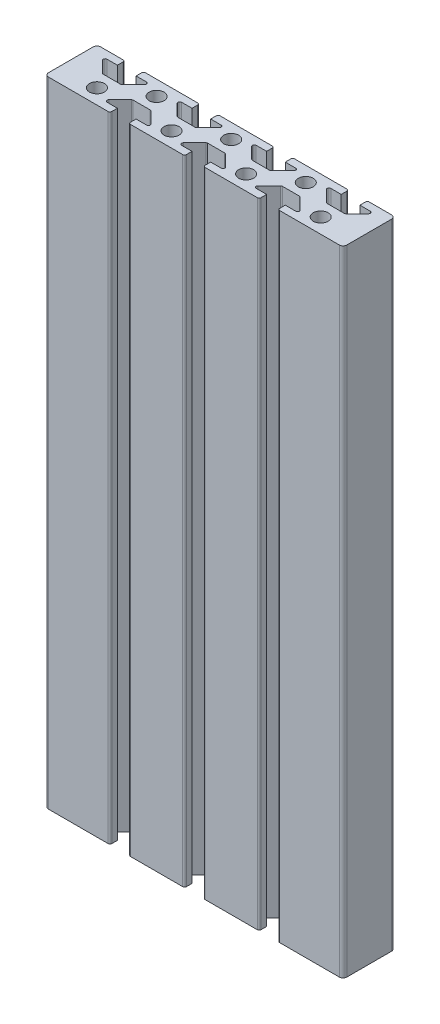
SolidWorks part; units mm, degrees
ref_plane "Front Plane" through (0, 0, 0) normal (0, 0, 1) x (1, 0, 0)
ref_plane "Top Plane" through (0, 0, 0) normal (0, 1, 0) x (1, 0, 0)
ref_plane "Right Plane" through (0, 0, 0) normal (1, 0, 0) x (0, 0, -1)
sketch "Sketch1" plane through (0, 0, 0) normal (0, 1, 0) x (1, 0, 0)
  line L0 (63.5, 12) -> (67.5, 12)
  line L1 (0, 0) -> (80, 0)
  line L2 (0, 0) -> (0, 14)
  line L3 (0, 14) -> (80, 14)
  line L4 (80, 0) -> (80, 14)
  line L5 (67.5, 12) -> (67.5, 14)
  line L6 (67.5, 14) -> (72.5, 14)
  line L7 (72.5, 14) -> (72.5, 12)
  line L9 (76.5, 12) -> (72.5, 8)
  line L10 (72.5, 8) -> (67.5, 8)
  line L11 (67.5, 8) -> (63.5, 12)
  line L12 (72.5, 12) -> (76.5, 12)
  line L13 (52.5, 12) -> (56.5, 12)
  line L14 (56.5, 12) -> (52.5, 8)
  line L15 (52.5, 8) -> (47.5, 8)
  line L16 (47.5, 8) -> (43.5, 12)
  line L17 (43.5, 12) -> (47.5, 12)
  line L18 (47.5, 12) -> (47.5, 14)
  line L19 (47.5, 14) -> (52.5, 14)
  line L20 (52.5, 14) -> (52.5, 12)
  line L21 (32.5, 12) -> (36.5, 12)
  line L22 (36.5, 12) -> (32.5, 8)
  line L23 (32.5, 8) -> (27.5, 8)
  line L24 (27.5, 8) -> (23.5, 12)
  line L25 (23.5, 12) -> (27.5, 12)
  line L26 (27.5, 12) -> (27.5, 14)
  line L27 (27.5, 14) -> (32.5, 14)
  line L28 (32.5, 14) -> (32.5, 12)
  line L29 (12.5, 12) -> (16.5, 12)
  line L30 (16.5, 12) -> (12.5, 8)
  line L31 (12.5, 8) -> (7.5, 8)
  line L32 (7.5, 8) -> (3.5, 12)
  line L33 (3.5, 12) -> (7.5, 12)
  line L34 (7.5, 12) -> (7.5, 14)
  line L35 (7.5, 14) -> (12.5, 14)
  line L36 (12.5, 14) -> (12.5, 12)
  line L37 (57.5, 0) -> (57.5, 2)
  line L38 (57.5, 2) -> (53.5, 2)
  line L39 (53.5, 2) -> (57.5, 6)
  line L40 (57.5, 6) -> (62.5, 6)
  line L41 (62.5, 6) -> (66.5, 2)
  line L42 (66.5, 2) -> (62.5, 2)
  line L43 (62.5, 2) -> (62.5, 0)
  line L44 (62.5, 0) -> (57.5, 0)
  line L45 (42.5, 0) -> (37.5, 0)
  line L46 (37.5, 0) -> (37.5, 2)
  line L47 (37.5, 2) -> (33.5, 2)
  line L48 (33.5, 2) -> (37.5, 6)
  line L49 (37.5, 6) -> (42.5, 6)
  line L50 (42.5, 6) -> (46.5, 2)
  line L51 (46.5, 2) -> (42.5, 2)
  line L52 (42.5, 2) -> (42.5, 0)
  line L53 (22.5, 0) -> (17.5, 0)
  line L54 (17.5, 0) -> (17.5, 2)
  line L55 (17.5, 2) -> (13.5, 2)
  line L56 (13.5, 2) -> (17.5, 6)
  line L57 (17.5, 6) -> (22.5, 6)
  line L58 (22.5, 6) -> (26.5, 2)
  line L59 (26.5, 2) -> (22.5, 2)
  line L60 (22.5, 2) -> (22.5, 0)
  circle A0 centre (60, 10) radius 2
  circle A1 centre (40, 10) radius 2
  circle A2 centre (20, 10) radius 2
  circle A3 centre (70, 4) radius 2
  circle A4 centre (50, 4) radius 2
  circle A5 centre (30, 4) radius 2
  circle A6 centre (10, 4) radius 2
  dimension "D17" = 4
  dimension "D21" = 4
  dimension "D1" = 80
  dimension "D2" = 14
  dimension "D3" = 7.5
  dimension "D4" = 5
  dimension "D5" = 6
  dimension "D6" = 17.5
  dimension "D7" = 2
  dimension "D8" = 4
  dimension "D9" = 5
  dimension "D10" = 5
  dimension "D11" = 4
  dimension "D12" = 4
  dimension "D13" = 2
  dimension "D14" = 2
  dimension "D15" = 6
  dimension "D16" = 3
  dimension "D18" = 20
  dimension "D19" = 4
  dimension "D22" = 10
  dimension "D23" = 4
  dimension "D20" = 3
  dimension "D24" = 4
extrude "Boss-Extrude1" add sketch "Sketch1" along normal blind 170 contours L59 L60 L1 L46 L47 L48 L49 L50 L51 L52 L37 L38 L39 L40 L41 L42 L43 L4 L3 L7 L12 L9 L10 L11 L0 L5 L20 L13 L14 L15 L16 L17 L18 L28 L21 L22 L23 L24 L25 L26 L36 L29 L30 L31 L32 L33
fillet "Fillet1" radius 0.5 24 edges at (67.5, 85, -8) (63.5, 85, -12) (76.5, 85, -12) (72.5, 85, -8) (47.5, 85, -8) (27.5, 85, -8) (52.5, 85, -8) (32.5, 85, -8) (56.5, 85, -12) (36.5, 85, -12) (43.5, 85, -12) (23.5, 85, -12) (12.5, 85, -8) (7.5, 85, -8) (3.5, 85, -12) (16.5, 85, -12) (72.5, 85, -14) (67.5, 85, -14) (52.5, 85, -14) (47.5, 85, -14) (32.5, 85, -14) (27.5, 85, -14) (12.5, 85, -14) (7.5, 85, -14)
fillet "Fillet2" radius 0.5 18 edges at (17.5, 85, -6) (26.5, 85, -2) (22.5, 85, -6) (22.5, 85, 0) (17.5, 85, 0) (13.5, 85, -2) (33.5, 85, -2) (37.5, 85, -6) (42.5, 85, -6) (42.5, 85, 0) (46.5, 85, -2) (37.5, 85, 0) (57.5, 85, 0) (62.5, 85, 0) (53.5, 85, -2) (57.5, 85, -6) (66.5, 85, -2) (62.5, 85, -6)
fillet "Fillet3" radius 1 4 edges at (0, 85, -14) (0, 85, 0) (80, 85, -14) (80, 85, 0)
sketch "Sketch2" plane through (0, 0, -14) normal (0, 0, -1) x (-1, 0, 0)
  line L0 (-33, 0) -> (-47, 0) construction
  circle A1 centre (-40, 10) radius 2.5
  dimension "D1" = 10
  dimension "D2" = 5
extrude "Cut-Extrude2" cut sketch "Sketch2" against normal blind 230 contours A1
sketch "Sketch3" plane through (0, 0, -14) normal (0, 0, -1) x (-1, 0, 0)
  circle A0 centre (-40, 10) radius 5.5
  dimension "D1" = 11
extrude "Cut-Extrude3" cut sketch "Sketch3" against normal blind 7 contours A0
sketch "Sketch4" plane through (0, 0, -14) normal (0, 0, -1) x (-1, 0, 0)
  line L0 (-33, 170) -> (-47, 170) construction
  circle A0 centre (-40, 160) radius 2.5
  dimension "D1" = 5
  dimension "D2" = 10
extrude "Cut-Extrude4" cut sketch "Sketch4" against normal blind 7
sketch "Sketch5" plane through (0, 0, -14) normal (0, 0, -1) x (-1, 0, 0)
  circle A0 centre (-40, 160) radius 5.5
  dimension "D1" = 11
extrude "Cut-Extrude5" cut sketch "Sketch5" against normal blind 7
